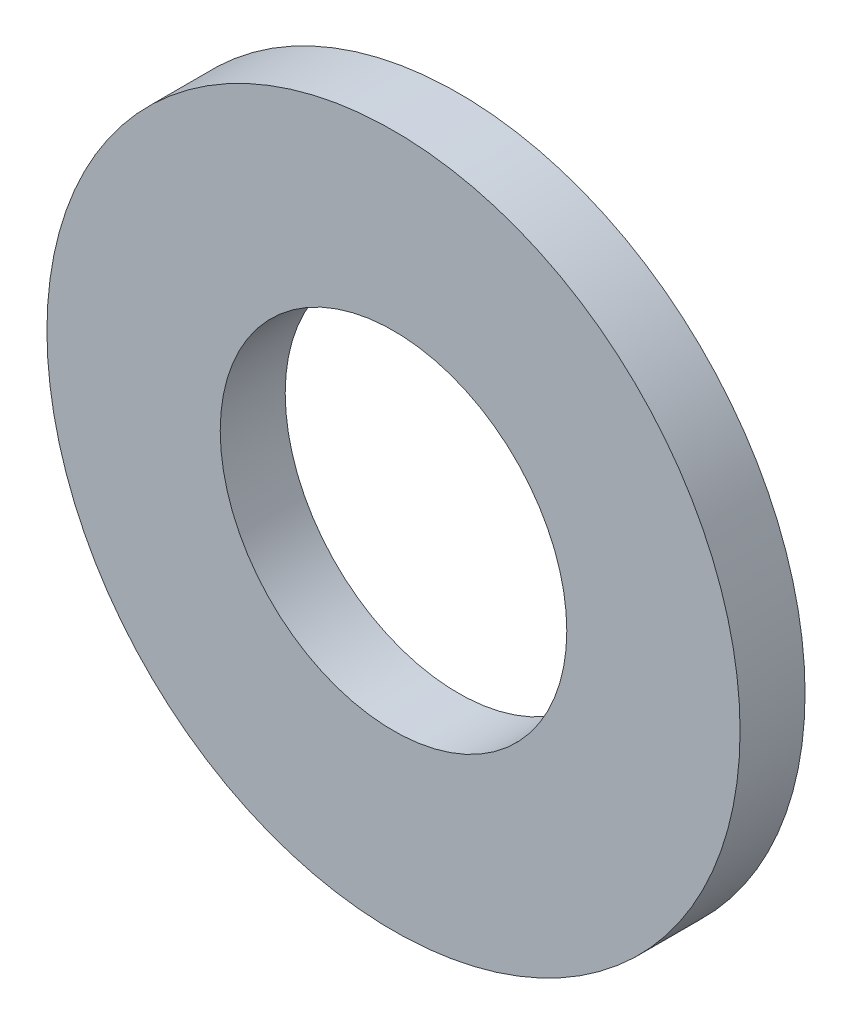
SolidWorks part; units mm, degrees
ref_plane "Front Plane" through (0, 0, 0) normal (0, 0, 1) x (1, 0, 0)
ref_plane "Top Plane" through (0, 0, 0) normal (0, 1, 0) x (1, 0, 0)
ref_plane "Right Plane" through (0, 0, 0) normal (1, 0, 0) x (0, 0, -1)
sketch "Sketch1" plane through (0, 0, 0) normal (0, 0, 1) x (1, 0, 0)
  circle A0 centre (0, 0) radius 8
  circle A1 centre (0, 0) radius 4
  dimension "D1" = 8
  dimension "D2" = 16
extrude "Boss-Extrude1" add sketch "Sketch1" along normal blind 1.5
